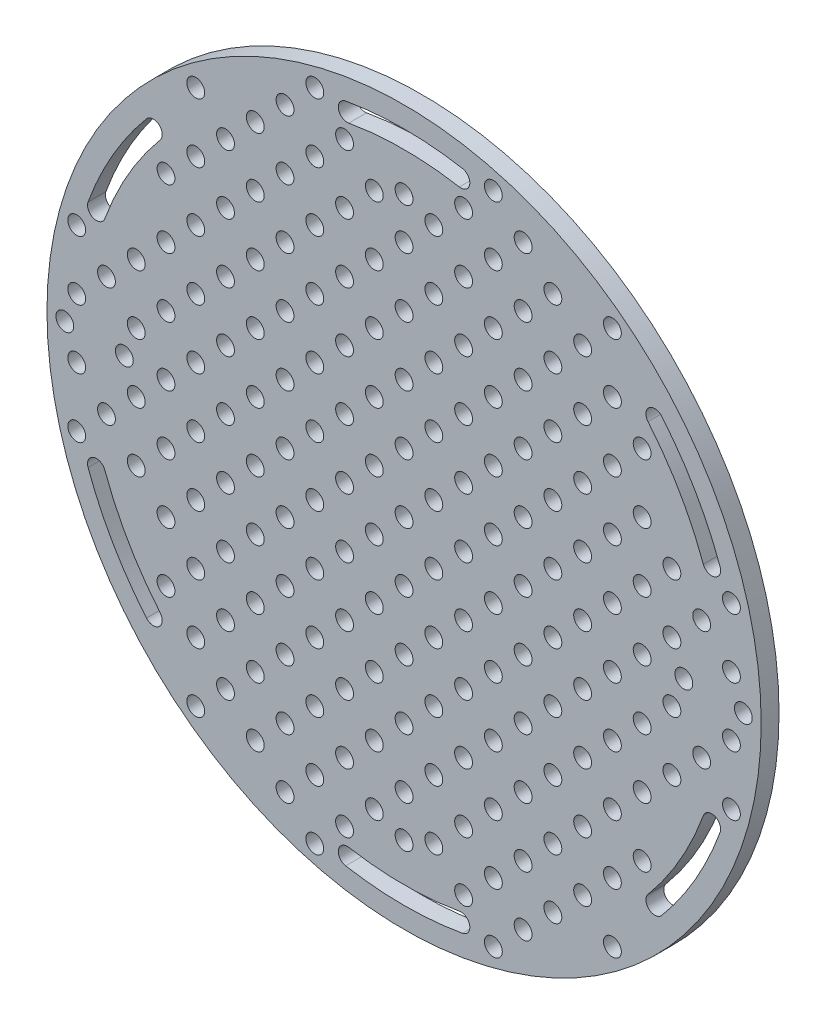
SolidWorks part; units mm, degrees
ref_plane "Plan de face" through (0, 0, 0) normal (0, 0, 1) x (1, 0, 0)
ref_plane "Plan de dessus" through (0, 0, 0) normal (0, 1, 0) x (1, 0, 0)
ref_plane "Plan de droite" through (0, 0, 0) normal (1, 0, 0) x (0, 0, -1)
sketch "Esquisse1" plane through (0, 0, 0) normal (0, 0, 1) x (1, 0, 0)
  circle A0 centre (0, 0) radius 50
  circle A1 centre (0, 47) radius 1.5
  circle A2 centre (47, 0) radius 1.5
  circle A3 centre (0, -47) radius 1.5
  circle A4 centre (-47, 0) radius 1.5
  point P14 (0, 0)
  dimension "D1" = 100
  dimension "D2" = 3
  dimension "D3" = 47
  dimension "D4" = 4
extrude "Boss.-Extru.1" add sketch "Esquisse1" along normal blind 3
sketch "Esquisse2" plane through (0, 0, 3) normal (0, 0, 1) x (1, 0, 0)
  circle A0 centre (0, 0) radius 60
  circle A1 centre (0, 0) radius 50
  dimension "D1" = 10
extrude "Boss.-Extru.2" add sketch "Esquisse2" against normal blind 3
sketch "Esquisse3" plane through (0, 0, 3) normal (0, 0, 1) x (1, 0, 0)
  line L0 (0, 60) -> (0, -60) construction
  line L1 (0, -60) -> (0, 0) construction
  line L2 (-60, 0) -> (60, 0) construction
  line L3 (60, 0) -> (-60, 0) construction
  circle A0 centre (0, 0) radius 1.5
  circle A1 centre (10, 0) radius 1.5
  circle A2 centre (20, 0) radius 1.5
  circle A3 centre (30, 0) radius 1.5
  circle A4 centre (40, 0) radius 1.5
  circle A7 centre (10, 10) radius 1.5
  circle A8 centre (20, 10) radius 1.5
  circle A9 centre (30, 10) radius 1.5
  circle A10 centre (40, 10) radius 1.5
  circle A13 centre (10, 20) radius 1.5
  circle A14 centre (20, 20) radius 1.5
  circle A15 centre (30, 20) radius 1.5
  circle A16 centre (40, 20) radius 1.5
  circle A19 centre (10, 30) radius 1.5
  circle A20 centre (20, 30) radius 1.5
  circle A21 centre (30, 30) radius 1.5
  circle A25 centre (10, 40) radius 1.5
  circle A26 centre (20, 40) radius 1.5
  circle A43 centre (0, 10) radius 1.5
  circle A44 centre (0, 20) radius 1.5
  circle A45 centre (0, 30) radius 1.5
  circle A46 centre (0, 40) radius 1.5
  circle A49 centre (50, 0) radius 1.5 [skipped]
  circle A50 centre (60, 0) radius 1.5 [skipped]
  circle A52 centre (0, 0) radius 60 construction
  circle A53 centre (50, 10) radius 1.5 [skipped]
  circle A54 centre (40, 40) radius 1.5 [skipped]
  circle A55 centre (50, 40) radius 1.5 [skipped]
  circle A56 centre (60, 40) radius 1.5 [skipped]
  circle A57 centre (40, 50) radius 1.5 [skipped]
  circle A58 centre (50, 50) radius 1.5 [skipped]
  circle A59 centre (60, 50) radius 1.5 [skipped]
  circle A60 centre (40, 60) radius 1.5 [skipped]
  circle A61 centre (50, 60) radius 1.5 [skipped]
  circle A62 centre (60, 60) radius 1.5 [skipped]
  circle A63 centre (10, 60) radius 1.5 [skipped]
  circle A64 centre (20, 60) radius 1.5 [skipped]
  circle A65 centre (30, 60) radius 1.5 [skipped]
  circle A66 centre (0, 60) radius 1.5 [skipped]
  circle A67 centre (60, 10) radius 1.5 [skipped]
  circle A68 centre (60, 20) radius 1.5 [skipped]
  circle A69 centre (60, 30) radius 1.5 [skipped]
  circle A70 centre (50, 30) radius 1.5 [skipped]
  circle A71 centre (50, 20) radius 1.5 [skipped]
  circle A72 centre (40, 30) radius 1.5 [skipped]
  circle A73 centre (30, 40) radius 1.5 [skipped]
  circle A74 centre (0, 50) radius 1.5 [skipped]
  circle A75 centre (10, 50) radius 1.5 [skipped]
  circle A76 centre (20, 50) radius 1.5 [skipped]
  circle A77 centre (30, 50) radius 1.5 [skipped]
  circle A78 centre (-20, 40) radius 1.5
  circle A79 centre (-10, 40) radius 1.5
  circle A80 centre (-30, 30) radius 1.5
  circle A81 centre (-20, 30) radius 1.5
  circle A82 centre (-10, 30) radius 1.5
  circle A83 centre (-40, 20) radius 1.5
  circle A84 centre (-30, 20) radius 1.5
  circle A85 centre (-20, 20) radius 1.5
  circle A86 centre (-10, 20) radius 1.5
  circle A87 centre (-40, 10) radius 1.5
  circle A88 centre (-30, 10) radius 1.5
  circle A89 centre (-20, 10) radius 1.5
  circle A90 centre (-10, 10) radius 1.5
  circle A91 centre (-40, 0) radius 1.5
  circle A92 centre (-30, 0) radius 1.5
  circle A93 centre (-20, 0) radius 1.5
  circle A94 centre (-10, 0) radius 1.5
  circle A95 centre (-10, -10) radius 1.5
  circle A96 centre (-20, -10) radius 1.5
  circle A97 centre (-30, -10) radius 1.5
  circle A98 centre (-40, -10) radius 1.5
  circle A99 centre (-10, -20) radius 1.5
  circle A100 centre (-20, -20) radius 1.5
  circle A101 centre (-30, -20) radius 1.5
  circle A102 centre (-40, -20) radius 1.5
  circle A103 centre (-10, -30) radius 1.5
  circle A104 centre (-20, -30) radius 1.5
  circle A105 centre (-30, -30) radius 1.5
  circle A106 centre (-10, -40) radius 1.5
  circle A107 centre (-20, -40) radius 1.5
  circle A108 centre (0, -40) radius 1.5
  circle A109 centre (0, -30) radius 1.5
  circle A110 centre (0, -20) radius 1.5
  circle A111 centre (0, -10) radius 1.5
  circle A112 centre (20, -40) radius 1.5
  circle A113 centre (10, -40) radius 1.5
  circle A114 centre (30, -30) radius 1.5
  circle A115 centre (20, -30) radius 1.5
  circle A116 centre (10, -30) radius 1.5
  circle A117 centre (40, -20) radius 1.5
  circle A118 centre (30, -20) radius 1.5
  circle A119 centre (20, -20) radius 1.5
  circle A120 centre (10, -20) radius 1.5
  circle A121 centre (40, -10) radius 1.5
  circle A122 centre (30, -10) radius 1.5
  circle A123 centre (20, -10) radius 1.5
  circle A124 centre (10, -10) radius 1.5
  dimension "D1" = 3
  dimension "D2" = 7
  dimension "D3" = 7
extrude "Enlèv. mat.-Extru.1" cut sketch "Esquisse3" against normal blind 3
sketch "Esquisse4" plane through (0, 0, 3) normal (0, 0, 1) x (1, 0, 0)
  line L0 (0, 0) -> (0, 55) construction
  line L1 (0, 55) -> (0, 0) construction
  line L2 (0, 0) -> (9.5506, 54.1644) construction
  line L3 (9.5506, 54.1644) -> (0, 0) construction
  line L4 (0, 0) -> (-9.5506, 54.1644) construction
  circle A0 centre (0, 0) radius 55
  circle A1 centre (0, 0) radius 60 construction
  arc A2 (-9.5506, 54.1644) -> (9.5506, 54.1644) centre (0, 0) cw construction
  arc A3 (9.8111, 55.6416) -> (-9.8111, 55.6416) centre (0, 0) ccw
  arc A4 (9.2902, 52.6872) -> (-9.2902, 52.6872) centre (0, 0) ccw
  arc A5 (9.2902, 52.6872) -> (9.8111, 55.6416) centre (9.5506, 54.1644) ccw
  arc A6 (-9.8111, 55.6416) -> (-9.2902, 52.6872) centre (-9.5506, 54.1644) ccw
  arc A7 (42.1324, 35.3533) -> (51.6831, 18.8111) centre (0, 0) cw construction
  arc A8 (53.0926, 19.3241) -> (43.2815, 36.3175) centre (0, 0) ccw
  arc A9 (50.2736, 18.2981) -> (40.9834, 34.3891) centre (0, 0) ccw
  arc A10 (50.2736, 18.2981) -> (53.0926, 19.3241) centre (51.6831, 18.8111) ccw
  arc A11 (43.2815, 36.3175) -> (40.9834, 34.3891) centre (42.1324, 35.3533) ccw
  arc A12 (51.6831, -18.8111) -> (42.1324, -35.3533) centre (0, 0) cw construction
  arc A13 (43.2815, -36.3175) -> (53.0926, -19.3241) centre (0, 0) ccw
  arc A14 (40.9834, -34.3891) -> (50.2736, -18.2981) centre (0, 0) ccw
  arc A15 (40.9834, -34.3891) -> (43.2815, -36.3175) centre (42.1324, -35.3533) ccw
  arc A16 (53.0926, -19.3241) -> (50.2736, -18.2981) centre (51.6831, -18.8111) ccw
  arc A17 (9.5506, -54.1644) -> (-9.5506, -54.1644) centre (0, 0) cw construction
  arc A18 (-9.8111, -55.6416) -> (9.8111, -55.6416) centre (0, 0) ccw
  arc A19 (-9.2902, -52.6872) -> (9.2902, -52.6872) centre (0, 0) ccw
  arc A20 (-9.2902, -52.6872) -> (-9.8111, -55.6416) centre (-9.5506, -54.1644) ccw
  arc A21 (9.8111, -55.6416) -> (9.2902, -52.6872) centre (9.5506, -54.1644) ccw
  arc A22 (-42.1324, -35.3533) -> (-51.6831, -18.8111) centre (0, 0) cw construction
  arc A23 (-53.0926, -19.3241) -> (-43.2815, -36.3175) centre (0, 0) ccw
  arc A24 (-50.2736, -18.2981) -> (-40.9834, -34.3891) centre (0, 0) ccw
  arc A25 (-50.2736, -18.2981) -> (-53.0926, -19.3241) centre (-51.6831, -18.8111) ccw
  arc A26 (-43.2815, -36.3175) -> (-40.9834, -34.3891) centre (-42.1324, -35.3533) ccw
  arc A27 (-51.6831, 18.8111) -> (-42.1324, 35.3533) centre (0, 0) cw construction
  arc A28 (-43.2815, 36.3175) -> (-53.0926, 19.3241) centre (0, 0) ccw
  arc A29 (-40.9834, 34.3891) -> (-50.2736, 18.2981) centre (0, 0) ccw
  arc A30 (-40.9834, 34.3891) -> (-43.2815, 36.3175) centre (-42.1324, 35.3533) ccw
  arc A31 (-53.0926, 19.3241) -> (-50.2736, 18.2981) centre (-51.6831, 18.8111) ccw
  point P9 (0, 55)
  point P19 (47.6314, 27.5)
  point P26 (47.6314, -27.5)
  point P33 (0, -55)
  point P40 (-47.6314, -27.5)
  point P47 (-47.6314, 27.5)
  point P52 (0, 0)
  dimension "D1" = 5
  dimension "D4" = 6
  dimension "D2" = 10
  dimension "D3" = 10
extrude "Enlèv. mat.-Extru.3" cut sketch "Esquisse4" against normal blind 3 contours A3 A6 A4 A5 | A28 A31 A29 A30 | A8 A11 A9 A10 | A13 A16 A14 A15 | A18 A21 A19 A20 | A23 A26 A24 A25
sketch "Esquisse10" plane through (0, 0, 0) normal (0, 0, -1) x (-1, 0, 0)
  line L0 (-60, 0) -> (60, 0) construction
  line L1 (0, -60) -> (0, 60) construction
  circle A3 centre (-10, 50) radius 1.5
  circle A6 centre (-20, 50) radius 1.5
  circle A7 centre (-30, 40) radius 1.5
  circle A11 centre (-30, 30) radius 1.5 construction
  circle A12 centre (-30, 30) radius 1.5 construction
  circle A13 centre (-20, 40) radius 1.5 construction
  circle A14 centre (-10, 40) radius 1.5 construction
  circle A15 centre (-40, 30) radius 1.5
  circle A18 centre (-50, 10) radius 1.5
  circle A19 centre (-40, 10) radius 1.5 construction
  circle A20 centre (-57, 0) radius 1.5
  circle A21 centre (-47, 0) radius 1.5 construction
  circle A22 centre (0, 0) radius 60 construction
  circle A23 centre (-50, -10) radius 1.5
  circle A24 centre (-40, -30) radius 1.5
  circle A25 centre (-30, -40) radius 1.5
  circle A26 centre (-20, -50) radius 1.5
  circle A27 centre (-10, -50) radius 1.5
  circle A28 centre (10, -50) radius 1.5
  circle A29 centre (20, -50) radius 1.5
  circle A30 centre (30, -40) radius 1.5
  circle A31 centre (40, -30) radius 1.5
  circle A32 centre (50, -10) radius 1.5
  circle A33 centre (57, 0) radius 1.5
  circle A34 centre (50, 10) radius 1.5
  circle A35 centre (40, 30) radius 1.5
  circle A36 centre (30, 40) radius 1.5
  circle A37 centre (20, 50) radius 1.5
  circle A38 centre (10, 50) radius 1.5
  point P43 (0, 0)
  dimension "D1" = 3
  dimension "D2" = 3
  dimension "D3" = 3
  dimension "D4" = 0
  dimension "D5" = 10
  dimension "D6" = 10
  dimension "D7" = 0
  dimension "D8" = 0
  dimension "D9" = 10
  dimension "D10" = 10
  dimension "D11" = 3
  dimension "D12" = 0
  dimension "D13" = 10
  dimension "D14" = 3
  dimension "D15" = 0
  dimension "D16" = 10
  dimension "D17" = 3
extrude "Enlèv. mat.-Extru.7" cut sketch "Esquisse10" against normal blind 3
sketch "Esquisse11" plane through (0, 0, 0) normal (0, 0, -1) x (-1, 0, 0)
  line L0 (0, 0) -> (-57, 0) construction
  line L1 (-57, 0) -> (0, 0) construction
  line L2 (0, -47) -> (0, 47) construction
  circle A1 centre (5, 5) radius 1.5
  circle A2 centre (0, 0) radius 1.5 construction
  circle A3 centre (15, 5) radius 1.5
  circle A4 centre (25, 5) radius 1.5
  circle A5 centre (35, 5) radius 1.5
  circle A6 centre (45, 5) radius 1.5
  circle A7 centre (55, 5) radius 1.5
  circle A8 centre (15, 15) radius 1.5
  circle A9 centre (25, 15) radius 1.5
  circle A10 centre (35, 15) radius 1.5
  circle A11 centre (45, 15) radius 1.5
  circle A12 centre (55, 15) radius 1.5
  circle A13 centre (15, 25) radius 1.5
  circle A14 centre (25, 25) radius 1.5
  circle A15 centre (35, 25) radius 1.5
  circle A16 centre (45, 25) radius 1.5 [skipped]
  circle A17 centre (55, 25) radius 1.5 [skipped]
  circle A18 centre (15, 35) radius 1.5
  circle A19 centre (25, 35) radius 1.5
  circle A20 centre (35, 35) radius 1.5
  circle A21 centre (45, 35) radius 1.5 [skipped]
  circle A22 centre (55, 35) radius 1.5 [skipped]
  circle A23 centre (15, 45) radius 1.5
  circle A24 centre (25, 45) radius 1.5
  circle A25 centre (35, 45) radius 1.5
  circle A26 centre (45, 45) radius 1.5 [skipped]
  circle A27 centre (55, 45) radius 1.5 [skipped]
  circle A28 centre (15, 55) radius 1.5
  circle A29 centre (25, 55) radius 1.5 [skipped]
  circle A30 centre (35, 55) radius 1.5 [skipped]
  circle A31 centre (45, 55) radius 1.5 [skipped]
  circle A32 centre (55, 55) radius 1.5 [skipped]
  circle A33 centre (5, 15) radius 1.5
  circle A34 centre (5, 25) radius 1.5
  circle A35 centre (5, 35) radius 1.5
  circle A36 centre (5, 45) radius 1.5
  circle A37 centre (5, 55) radius 1.5 [skipped]
  circle A38 centre (-5, 45) radius 1.5
  circle A39 centre (-5, 35) radius 1.5
  circle A40 centre (-5, 25) radius 1.5
  circle A41 centre (-5, 15) radius 1.5
  circle A42 centre (-15, 55) radius 1.5
  circle A43 centre (-35, 45) radius 1.5
  circle A44 centre (-25, 45) radius 1.5
  circle A45 centre (-15, 45) radius 1.5
  circle A46 centre (-35, 35) radius 1.5
  circle A47 centre (-25, 35) radius 1.5
  circle A48 centre (-15, 35) radius 1.5
  circle A49 centre (-35, 25) radius 1.5
  circle A50 centre (-25, 25) radius 1.5
  circle A51 centre (-15, 25) radius 1.5
  circle A52 centre (-55, 15) radius 1.5
  circle A53 centre (-45, 15) radius 1.5
  circle A54 centre (-35, 15) radius 1.5
  circle A55 centre (-25, 15) radius 1.5
  circle A56 centre (-15, 15) radius 1.5
  circle A57 centre (-55, 5) radius 1.5
  circle A58 centre (-45, 5) radius 1.5
  circle A59 centre (-35, 5) radius 1.5
  circle A60 centre (-25, 5) radius 1.5
  circle A61 centre (-15, 5) radius 1.5
  circle A62 centre (-5, 5) radius 1.5
  circle A63 centre (-5, -5) radius 1.5
  circle A64 centre (-15, -5) radius 1.5
  circle A65 centre (-25, -5) radius 1.5
  circle A66 centre (-35, -5) radius 1.5
  circle A67 centre (-45, -5) radius 1.5
  circle A68 centre (-55, -5) radius 1.5
  circle A69 centre (-15, -15) radius 1.5
  circle A70 centre (-25, -15) radius 1.5
  circle A71 centre (-35, -15) radius 1.5
  circle A72 centre (-45, -15) radius 1.5
  circle A73 centre (-55, -15) radius 1.5
  circle A74 centre (-15, -25) radius 1.5
  circle A75 centre (-25, -25) radius 1.5
  circle A76 centre (-35, -25) radius 1.5
  circle A77 centre (-15, -35) radius 1.5
  circle A78 centre (-25, -35) radius 1.5
  circle A79 centre (-35, -35) radius 1.5
  circle A80 centre (-15, -45) radius 1.5
  circle A81 centre (-25, -45) radius 1.5
  circle A82 centre (-35, -45) radius 1.5
  circle A83 centre (-15, -55) radius 1.5
  circle A84 centre (-5, -15) radius 1.5
  circle A85 centre (-5, -25) radius 1.5
  circle A86 centre (-5, -35) radius 1.5
  circle A87 centre (-5, -45) radius 1.5
  circle A88 centre (5, -45) radius 1.5
  circle A89 centre (5, -35) radius 1.5
  circle A90 centre (5, -25) radius 1.5
  circle A91 centre (5, -15) radius 1.5
  circle A92 centre (15, -55) radius 1.5
  circle A93 centre (35, -45) radius 1.5
  circle A94 centre (25, -45) radius 1.5
  circle A95 centre (15, -45) radius 1.5
  circle A96 centre (35, -35) radius 1.5
  circle A97 centre (25, -35) radius 1.5
  circle A98 centre (15, -35) radius 1.5
  circle A99 centre (35, -25) radius 1.5
  circle A100 centre (25, -25) radius 1.5
  circle A101 centre (15, -25) radius 1.5
  circle A102 centre (55, -15) radius 1.5
  circle A103 centre (45, -15) radius 1.5
  circle A104 centre (35, -15) radius 1.5
  circle A105 centre (25, -15) radius 1.5
  circle A106 centre (15, -15) radius 1.5
  circle A107 centre (55, -5) radius 1.5
  circle A108 centre (45, -5) radius 1.5
  circle A109 centre (35, -5) radius 1.5
  circle A110 centre (25, -5) radius 1.5
  circle A111 centre (15, -5) radius 1.5
  circle A112 centre (5, -5) radius 1.5
  dimension "D1" = 3
  dimension "D2" = 5
  dimension "D3" = 5
  dimension "D4" = 6
  dimension "D5" = 6
extrude "Enlèv. mat.-Extru.8" cut sketch "Esquisse11" against normal blind 3
